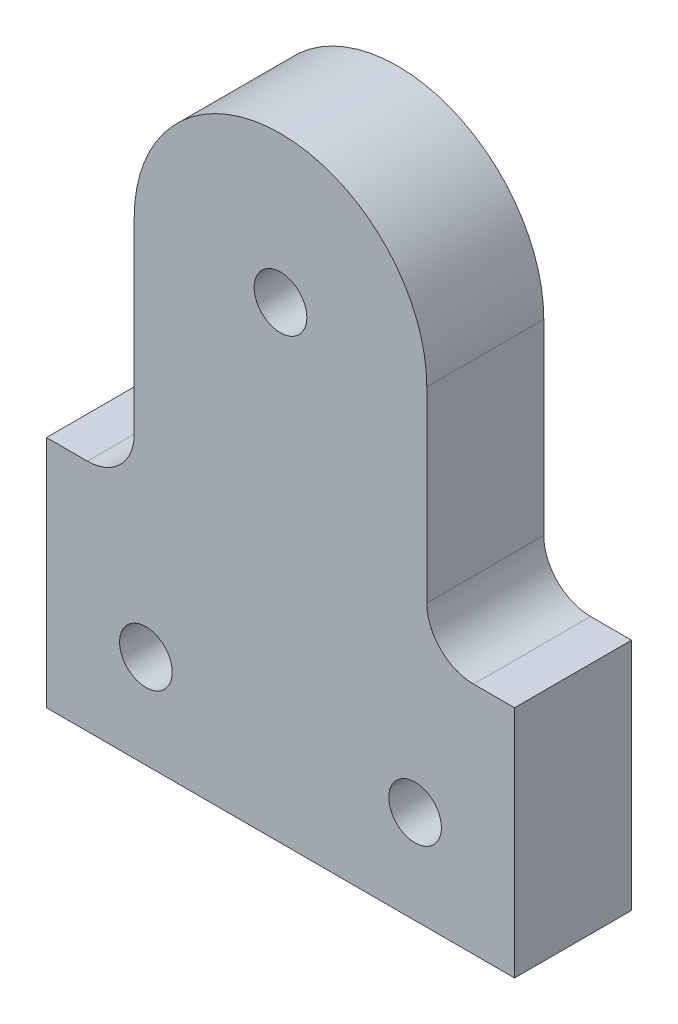
SolidWorks part; units mm, degrees
ref_plane "前视基准面" through (0, 0, 0) normal (0, 0, 1) x (1, 0, 0)
ref_plane "上视基准面" through (0, 0, 0) normal (0, 1, 0) x (1, 0, 0)
ref_plane "右视基准面" through (0, 0, 0) normal (1, 0, 0) x (0, 0, -1)
sketch "草图1" plane through (0, 0, 0) normal (0, 0, 1) x (1, 0, 0)
  line L0 (-38.6395, 0) -> (42.3129, 0) construction
  line L2 (-20, 12) -> (-20, -8)
  line L3 (-20, -8) -> (20, -8)
  line L4 (20, 12) -> (20, -8)
  line L5 (0, 29.446) -> (0, -27.833) construction
  line L6 (-12.5, 32) -> (-12.5, 16)
  line L7 (-16.5, 12) -> (-20, 12)
  line L8 (12.5, 32) -> (12.5, 16)
  line L9 (16.5, 12) -> (20, 12)
  circle A0 centre (-11.5, 0) radius 2.25
  circle A1 centre (11.5, 0) radius 2.25
  circle A3 centre (0, 32) radius 2.25
  arc A4 (12.5, 32) -> (-12.5, 32) centre (0, 32) ccw
  arc A5 (16.5, 12) -> (12.5, 16) centre (16.5, 16) cw
  arc A6 (-16.5, 12) -> (-12.5, 16) centre (-16.5, 16) ccw
  point P21 (12.5, 12)
  point P24 (-12.5, 12)
  dimension "D2" = 23
  dimension "D3" = 4.5
  dimension "D6" = 4.5
  dimension "D7" = 25
  dimension "D9" = 4
  dimension "D1" = 40
  dimension "D4" = 20
  dimension "D5" = 8
  dimension "D8" = 20
extrude "凸台-拉伸1" add sketch "草图1" along normal blind 10
sketch "草图2" plane through (0, 0, 0) normal (0, 0, -1) x (-1, 0, 0)
  line L1 (-11.5, -4.3301) -> (-7.75, -2.1651)
  line L2 (-7.75, -2.1651) -> (-7.75, 2.1651)
  line L3 (-7.75, 2.1651) -> (-11.5, 4.3301)
  line L4 (-11.5, 4.3301) -> (-15.25, 2.1651)
  line L5 (-15.25, 2.1651) -> (-15.25, -2.1651)
  line L6 (-15.25, -2.1651) -> (-11.5, -4.3301)
  line L7 (11.5, -4.3301) -> (15.25, -2.1651)
  line L8 (15.25, -2.1651) -> (15.25, 2.1651)
  line L9 (15.25, 2.1651) -> (11.5, 4.3301)
  line L10 (11.5, 4.3301) -> (7.75, 2.1651)
  line L11 (7.75, 2.1651) -> (7.75, -2.1651)
  line L12 (7.75, -2.1651) -> (11.5, -4.3301)
  circle A0 centre (-11.5, 0) radius 3.75 construction
  circle A1 centre (11.5, 0) radius 3.75 construction
  dimension "D1" = 7.5
  dimension "D2" = 7.5
extrude "切除-拉伸1" cut sketch "草图2" against normal blind 3
